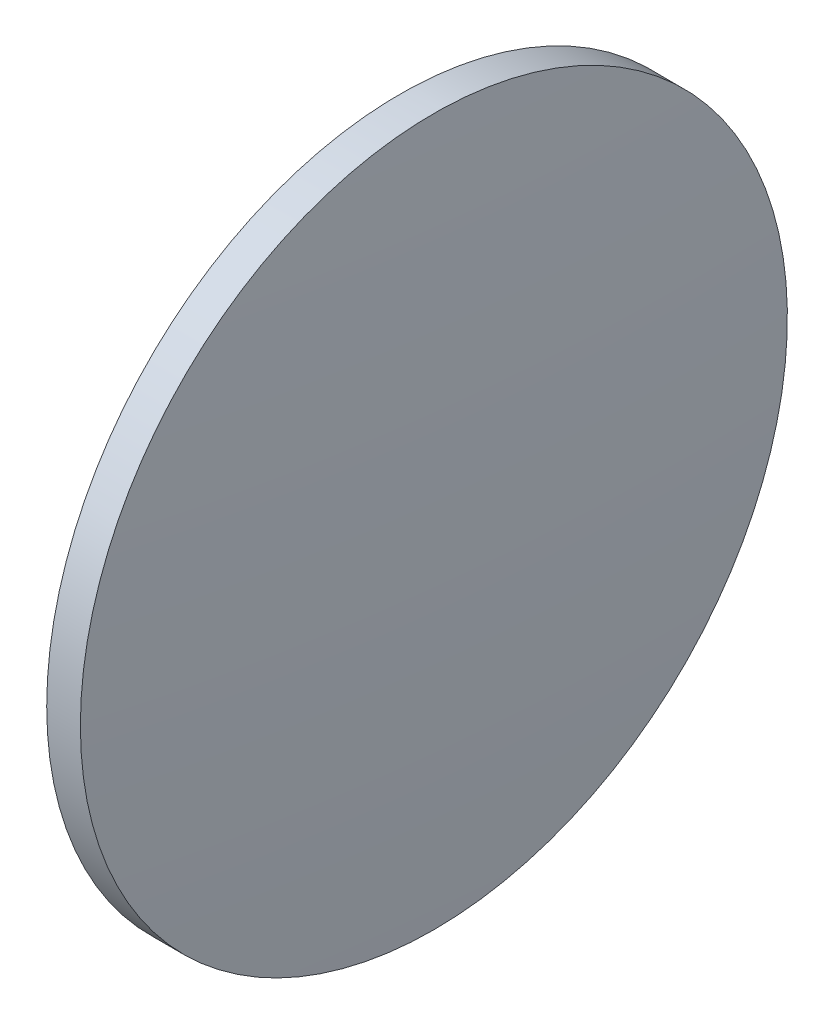
SolidWorks part; units mm, degrees
ref_plane "前视基准面" through (0, 0, 0) normal (0, 0, 1) x (1, 0, 0)
ref_plane "上视基准面" through (0, 0, 0) normal (0, 1, 0) x (1, 0, 0)
ref_plane "右视基准面" through (0, 0, 0) normal (1, 0, 0) x (0, 0, -1)
sketch "草图1" plane through (0, 0, 0) normal (0, 0, 1) x (1, 0, 0)
  line L0 (218.1237, 130.5186) -> (243.8524, 130.5186) construction
  line L1 (226.8933, 130.5186) -> (226.8933, 162.0186)
  line L2 (226.8933, 162.0186) -> (229.8933, 162.0186)
  line L3 (230.8533, 130.5186) -> (226.8933, 130.5186)
  arc A0 (230.8533, 130.5186) -> (229.8933, 162.0186) centre (-286.4236, 130.5186) ccw
revolve "旋转1" add sketch "草图1" angle 360 about L0
